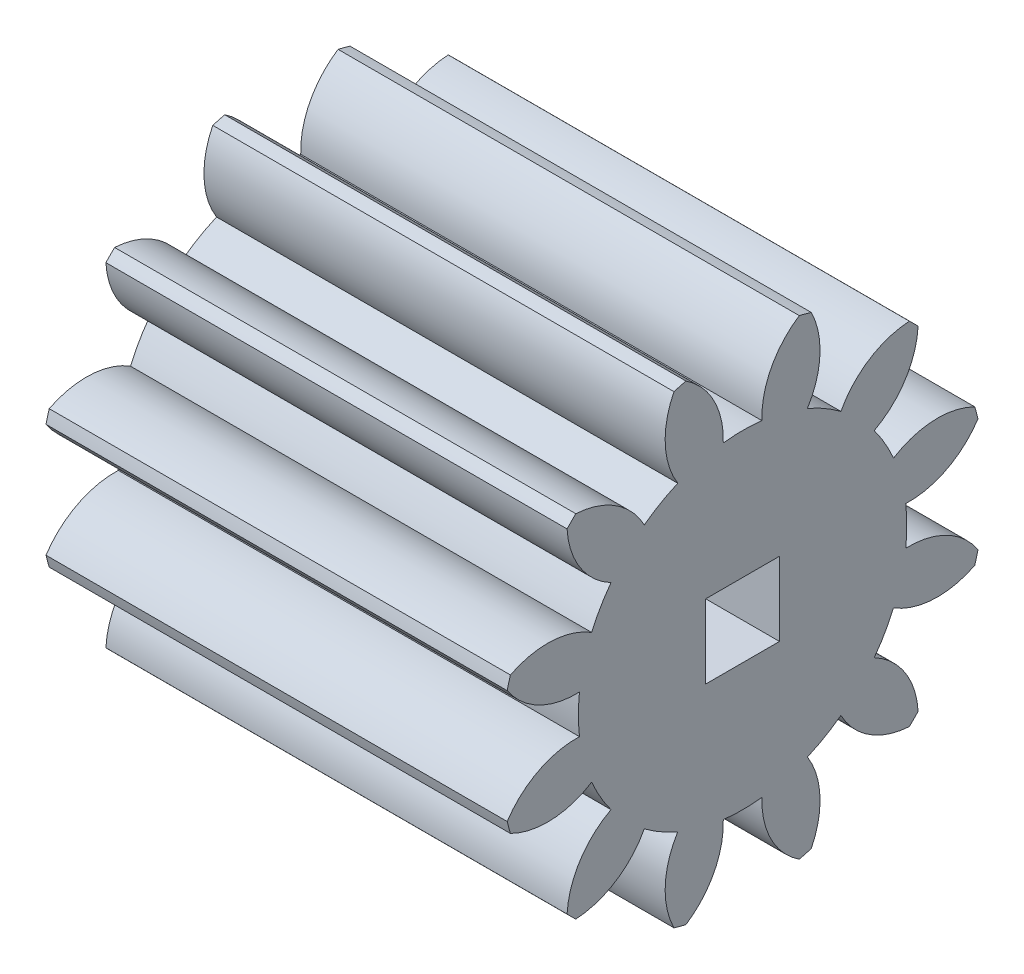
SolidWorks part; units mm, degrees
ref_plane "Plane1" through (0, 0, 0) normal (0, 0, 1) x (1, 0, 0)
ref_plane "Plane2" through (0, 0, 0) normal (0, 1, 0) x (1, 0, 0)
ref_plane "Plane3" through (0, 0, 0) normal (1, 0, 0) x (0, 0, -1)
other "Configuration Table"
sketch "HoldingSke" plane through (0, 0, 0) normal (0, 1, 0) x (1, 0, 0)
  line L0 (0, 0) -> (0.6521, -0.1386)
  line L1 (-15, 0) -> (100, 0) construction
  line L2 (0, 0) -> (-2.1039, 2.3779)
  line L3 (0, 0) -> (-11.863, 4.5341)
  line L4 (0, 0) -> (8.4473, 1.7955)
  line L5 (0, 0) -> (-46.8476, -17.4728)
  line L6 (0, 0) -> (-16.5793, -11.1861)
  line L7 (-2.1039, 2.3779) -> (8.6586, 51.2059)
  line L8 (-76.2, 54.61) -> (-76.1, 54.61)
  line L9 (-71.009, 38.7566) -> (-53.1078, 45.2721)
  line L10 (-76.2, 71.12) -> (104.1128, 71.12)
  line L11 (0, 0) -> (-20, 0)
  line L12 (-76.2, 101.6) -> (-76.147, 101.6)
  line L13 (24.9733, 27.94) -> (52.9518, 28.4284)
  line L14 (24.9733, 27.94) -> (24.9743, 27.94)
  line L15 (24.9733, 27.94) -> (100.4006, 29.5858)
  line L16 (-63.627, -1.5) -> (-12.827, -1.5)
  circle A0 centre (0, 0) radius 0.5
  circle A1 centre (0, 0) radius 7.124
  circle A2 centre (0, 0) radius 37.5
  circle A3 centre (0, 0) radius 0.5
  dimension "MHD" = 14.248
  dimension "Hub_dia" = 75
  dimension "Bore" = 1
  dimension "MBD" = 1
  dimension "Num_teeth" = 12
  dimension "Pitch" = 0.6667
  dimension "Overall_len" = 50
  dimension "Show_teeth" = 12
  dimension "Thickness" = 20
  dimension "OAL" = 50.0001
  dimension "T_dim" = 0.1
  dimension "Ap" = 20
  dimension "H" = 19.05
  dimension "Pitch_radius" = 180.3128
  dimension "Width" = 20
  dimension "Backlash" = 0.053
  dimension "Addendum_fac" = 1
  dimension "Dedendum_fac" = 1.25
  dimension "Clearance_fac" = 0.25
  dimension "Dedendum_add" = 0.001
  dimension "Module" = 1.5
sketch "BasProSke" plane through (0, 0, 0) normal (0, 1, 0) x (1, 0, 0)
  line L0 (-10, 0) -> (60, 0) construction
  line L1 (0, 0) -> (0, 10.5)
  line L2 (0, 0) -> (20, 0)
  line L3 (20, 0) -> (20, 10.5)
  line L4 (20, 10.5) -> (0, 10.5)
  dimension "Thickness" = 20
  dimension "Diameter" = 21
revolve "Base-Revolve" add sketch "BasProSke" angle 360 about L0
sketch "TooCutSke" plane through (0, 0, 0) normal (1, 0, 0) x (0, 0, -1)
  line L1 (0, 0) -> (0, 107) construction
  line L2 (0, 0) -> (-1.2674, 8.9103) construction
  line L3 (0, 0) -> (-4.625, 17.2606) construction
  line L4 (-1.2674, 8.9103) -> (-2.3125, 8.6303) construction
  arc A0 (0.8378, 7.0746) -> (-0.8378, 7.0746) centre (0, 0) ccw
  arc A1 (2.4865, 10.2275) -> (-2.4865, 10.2275) centre (0, 0) ccw
  circle A2 centre (0, 0) radius 9 construction
  circle A3 centre (0, 0) radius 8.4572 construction
  arc A4 (-0.8378, 7.0746) -> (-2.4865, 10.2275) centre (-4.4355, 7.2007) ccw
  arc A5 (2.4865, 10.2275) -> (0.8378, 7.0746) centre (4.4355, 7.2007) ccw
  dimension "Root_dia" = 14.248
  dimension "Overcut_dia" = 21.0508
  dimension "Pitch_dia" = 18
  dimension "Base_dia" = 16.9145
  dimension "Flank_rad" = 3.6
  dimension "Half_ang" = 15
  dimension "Half_CT" = 1.082
extrude "ToothCut" cut sketch "TooCutSke" along normal through all
fillet "Breaks" [suppressed] radius 0.03
fillet "RootFillets" [suppressed] radius 0.376
pattern_circular "TeethCuts" count 12 every 30 about axis through (-10, 0, 0) along (1, 0, 0) of "ToothCut", "RootFillets", "Breaks"
sketch "HubNeaOneSke" plane through (0, 0, 0) normal (-1, 0, 0) x (0, 0, 1)
  circle A0 centre (0, 0) radius 7.124
  dimension "Diameter" = 14.248
extrude "HubNearOne" [suppressed] add sketch "HubNeaOneSke" along normal blind 30.0001
sketch "HubNeaBotSke" plane through (0, 0, 0) normal (-1, 0, 0) x (0, 0, 1)
  circle A0 centre (0, 0) radius 7.124
  dimension "Diameter" = 14.248
extrude "HubNearBoth" [suppressed] add sketch "HubNeaBotSke" along normal blind 15
ref_plane "FarPln" through (20, 0, 0) normal (1, 0, 0) x (0, 0, -1)
sketch "HubFarSke" plane through (20, 0, 0) normal (1, 0, 0) x (0, 0, -1)
  circle A0 centre (0, 0) radius 7.124
  dimension "Diameter" = 14.248
extrude "HubFar" [suppressed] add sketch "HubFarSke" along normal blind 15
sketch "BorSke" plane through (0, 0, 0) normal (1, 0, 0) x (0, 0, -1)
  circle A0 centre (0, 0) radius 0.5
  dimension "Diameter" = 1
extrude "Bore" cut sketch "BorSke" along normal mid plane 100.0001
sketch "KeySke" plane through (0, 0, 0) normal (1, 0, 0) x (0, 0, -1)
  line L0 (-0.05, 0) -> (-0.05, 0.6)
  line L1 (-0.05, 0.6) -> (0.05, 0.6)
  line L2 (0.05, 0.6) -> (0.05, 0)
  line L3 (0, 0) -> (0, 34) construction
  line L4 (-0.05, 0) -> (0.05, 0)
  dimension "Offset" = 0.6
  dimension "Width" = 0.1
extrude "Keyway" [suppressed] cut sketch "KeySke" along normal mid plane 100.0001
pattern_circular "Keyway2" [suppressed] count 2 every 90 about axis through (-10, 0, 0) along (1, 0, 0)
sketch "Sketch1" plane through (20, 0, 0) normal (1, 0, 0) x (0, 0, -1)
  line L1 (-1.6, -1.6) -> (1.6, -1.6)
  line L2 (-1.6, -1.6) -> (-1.6, 1.6)
  line L3 (-1.6, 1.6) -> (1.6, 1.6)
  line L4 (1.6, -1.6) -> (1.6, 1.6)
  line L5 (-1.6, -1.6) -> (1.6, 1.6) construction
  line L6 (-1.6, 1.6) -> (1.6, -1.6) construction
  point P0 (0, 0)
  dimension "D1" = 3.2
  dimension "D2" = 3.2
extrude "Cut-Extrude1" cut sketch "Sketch1" against normal blind 30
sketch "Sketch3" plane through (0, 0, 0) normal (0, 1, 0) x (1, 0, 0)
  line L0 (0, 0) -> (10, 0) construction
  line L1 (0, -0.8378) -> (0, 0.8378) construction
  line L2 (10, 0) -> (10, 10) construction
  circle A0 centre (10, 0) radius 3.5
  point P0 (10, 0)
  dimension "D1" = 7
  dimension "D2" = 10
  dimension "D3" = 10
equation "' \"Module@HoldingSke\" = 6.35"
equation "' \"Num_teeth@HoldingSke\" = 12"
equation "' \"Ap@HoldingSke\" =  20"
equation "' \"Ap@HoldingSke\" = 20"
equation "' \"Width@HoldingSke\" = 0.5 * 25.4"
equation "' \"Hub_dia@HoldingSke\"= 1 * 25.4"
equation "' \"Hub_dia@HoldingSke\" = 1 * 25.4"
equation "' \"Overall_len@HoldingSke\" = 1.0 * 25.4"
equation "' \"Bore@HoldingSke\" = 0.75 * 25.4"
equation "' \"T_dim@HoldingSke\" = 0.1 * 25.4"
equation "' \"Width@KeySke\" = 0.25 * 25.4"
equation "' \"Show_teeth@HoldingSke\" = 13"
equation "' \"Backlash@HoldingSke\" = 0.009 * 25.4"
equation "' \"Addendum_fac@HoldingSke\" = 1.0"
equation "' \"Dedendum_fac@HoldingSke\" = 1.25"
equation "' \"Dedendum_add@HoldingSke\" = 0.00005 * 25.4"
equation "' \"Clearance_fac@HoldingSke\" = 0.25"
equation "\"Pitch@HoldingSke\" = 1 / \"Module@HoldingSke\""
equation "\"Overcut_dia@TooCutSke\" = (\"Num_teeth@HoldingSke\" + 2 * \"Addendum_fac@HoldingSke\") / \"Pitch@HoldingSke\" + 0.002 * 25.4"
equation "\"Pitch_dia@TooCutSke\" = \"Num_teeth@HoldingSke\" / \"Pitch@HoldingSke\""
equation "\"Base_dia@TooCutSke\" = \"Num_teeth@HoldingSke\" / \"Pitch@HoldingSke\" * cos((\"Ap@HoldingSke\"  * 3.14159265 / 180))"
equation "\"Root_dia@TooCutSke\" = (\"Num_teeth@HoldingSke\" + 2) / \"Pitch@HoldingSke\" - 2 * (\"Addendum_fac@HoldingSke\" + \"Dedendum_fac@HoldingSke\") / \"Pitch@HoldingSke\" - \"Dedendum_add@HoldingSke\" * 2"
equation "\"Half_ang@TooCutSke\" = 180 / \"Num_teeth@HoldingSke\""
equation "\"Half_CT@TooCutSke\" = \"Num_teeth@HoldingSke\" / \"Pitch@HoldingSke\" * sin((3.14159265 / 2 / \"Num_teeth@HoldingSke\")) / 2 - 7 * \"Backlash@HoldingSke\" / 4"
equation "\"Flank_rad@TooCutSke\" = \"Num_teeth@HoldingSke\" / \"Pitch@HoldingSke\" / 5"
equation "\"Radius@RootFillets\" = \"Clearance_fac@HoldingSke\" / \"Pitch@HoldingSke\" + \"Dedendum_add@HoldingSke\""
equation "\"Break_rad@Breaks\" = 0.02 / \"Pitch@HoldingSke\""
equation "\"Thickness@HoldingSke\" = \"Width@HoldingSke\""
equation "\"OAL@HoldingSke\" = \"Thickness@HoldingSke\""
equation "\"MHD@HoldingSke\" = (\"Num_teeth@HoldingSke\" + 2) / \"Pitch@HoldingSke\" - 2 * (\"Addendum_fac@HoldingSke\" + \"Dedendum_fac@HoldingSke\")  / \"Pitch@HoldingSke\" - \"Dedendum_add@HoldingSke\" * 2"
equation "\"MBD@HoldingSke\" = (\"Num_teeth@HoldingSke\" + 2) / \"Pitch@HoldingSke\" - 2 * (\"Addendum_fac@HoldingSke\" + \"Dedendum_fac@HoldingSke\")  / \"Pitch@HoldingSke\" - \"Dedendum_add@HoldingSke\" * 2 - 0.002 * 25.4"
equation "\"MHD@HoldingSke\" = ((sgn( \"MHD@HoldingSke\" - \"Hub_dia@HoldingSke\" )-1)*( \"MHD@HoldingSke\" - \"Hub_dia@HoldingSke\" ))/-2+ \"Hub_dia@HoldingSke\""
equation "\"MBD@HoldingSke\" = ((sgn( \"MBD@HoldingSke\" - \"Bore@HoldingSke\" )-1)*( \"MBD@HoldingSke\" - \"Bore@HoldingSke\" ))/-2+ \"Bore@HoldingSke\""
equation "\"OAL@HoldingSke\" = ((sgn( \"OAL@HoldingSke\" - \"Overall_len@HoldingSke\" )+1)*( \"OAL@HoldingSke\" - \"Overall_len@HoldingSke\" ))/2 + \"Overall_len@HoldingSke\" + 0.000002 * 25.4"
equation "\"Num_teeth@TeethCuts\" = int( \"Show_teeth@HoldingSke\" ) + 1"
equation "\"Num_teeth@TeethCuts\" = ((sgn( \"Num_teeth@TeethCuts\" - \"Num_teeth@HoldingSke\" )-1)*( \"Num_teeth@TeethCuts\" - \"Num_teeth@HoldingSke\" ))/-2+ \"Num_teeth@HoldingSke\""
equation "\"Num_teeth@TeethCuts\" = ((sgn( \"Num_teeth@TeethCuts\" - 2.0)+1)*( \"Num_teeth@TeethCuts\" - 2.0))/2 +2.0"
equation "\"Angle@TeethCuts\" = 360.0 / \"Num_teeth@HoldingSke\""
equation "\"Diameter@BasProSke\" = (\"Num_teeth@HoldingSke\" + 2 * \"Addendum_fac@HoldingSke\") / \"Pitch@HoldingSke\""
equation "' \"Fillet_rad@BasProSke\" =  \"Thickness@HoldingSke\" * 0.05"
equation "' \"Fillet_rad@BasProSke\" = \"Thickness@HoldingSke\" * 0.05"
equation "\"MHD@HoldingSke\" = ((sgn( \"MHD@HoldingSke\" - \"Root_dia@TooCutSke\" )-1)*( \"MHD@HoldingSke\" - \"Root_dia@TooCutSke\" ))/-2+ \"Root_dia@TooCutSke\""
equation "\"Diameter@HubNeaOneSke\" = \"MHD@HoldingSke\""
equation "\"Length@HubNearOne\" = \"OAL@HoldingSke\" - \"Thickness@BasProSke\""
equation "\"Diameter@HubNeaBotSke\" = \"MHD@HoldingSke\""
equation "\"Length@HubNearBoth\" = ( \"OAL@HoldingSke\" - \"Thickness@BasProSke\" ) / 2.0"
equation "\"Thickness@FarPln\" = \"Thickness@BasProSke\""
equation "\"Diameter@HubFarSke\" = \"MHD@HoldingSke\""
equation "\"Length@HubFar\" = ( \"OAL@HoldingSke\" - \"Thickness@BasProSke\" ) / 2.0"
equation "\"Diameter@BorSke\" = \"MBD@HoldingSke\""
equation "\"D1@Bore\" = \"OAL@HoldingSke\" * 2.0"
equation "\"D1@Keyway\" = \"OAL@HoldingSke\" * 2.0"
equation "\"Offset@KeySke\" = \"T_dim@HoldingSke\" + \"MBD@HoldingSke\" / 2.0"
